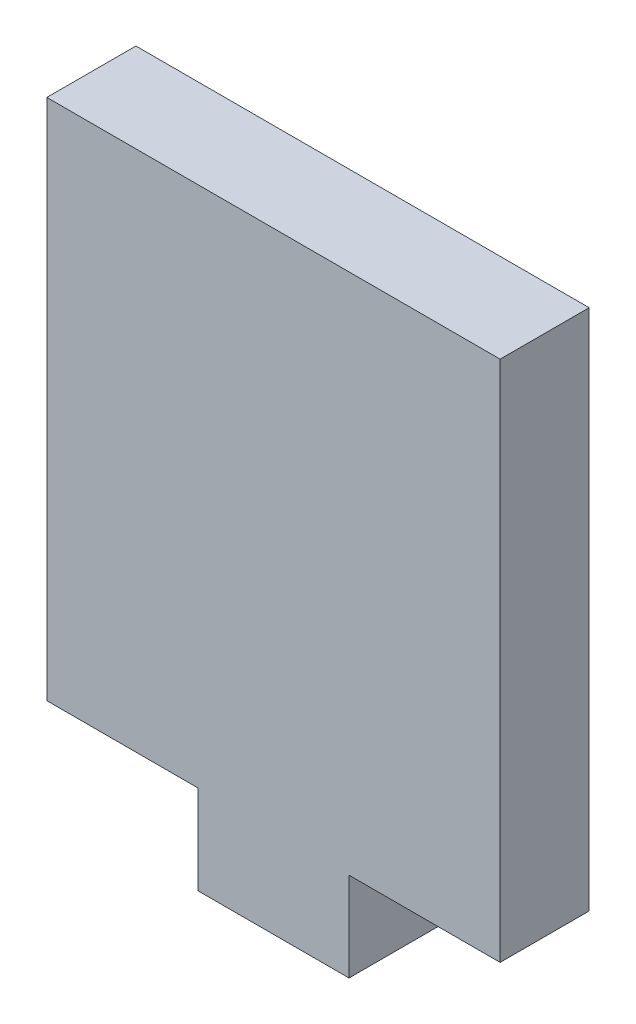
SolidWorks part; units mm, degrees
ref_plane "Front" through (0, 0, 0) normal (0, 0, 1) x (1, 0, 0)
ref_plane "Top" through (0, 0, 0) normal (0, 1, 0) x (1, 0, 0)
ref_plane "Right" through (0, 0, 0) normal (1, 0, 0) x (0, 0, -1)
sketch "Sketch1" plane through (0, 0, 0) normal (0, 0, 1) x (1, 0, 0)
  line L0 (-41.4918, 260.9985) -> (-10.9518, 260.9985)
  line L1 (-10.9518, 260.9985) -> (-10.9518, 225.7985)
  line L2 (-10.9518, 225.7985) -> (-21.1318, 225.7985)
  line L4 (-21.1318, 225.7985) -> (-21.1318, 219.7985)
  line L6 (-21.1318, 219.7985) -> (-31.3118, 219.7985)
  line L7 (-31.3118, 219.7985) -> (-31.3118, 225.7985)
  line L8 (-31.3118, 225.7985) -> (-41.4918, 225.7985)
  line L9 (-41.4918, 225.7985) -> (-41.4918, 260.9985)
  dimension "D1" = 10.18
  dimension "D2" = 10.18
extrude "Boss-Extrude1" add sketch "Sketch1" along normal blind 6
